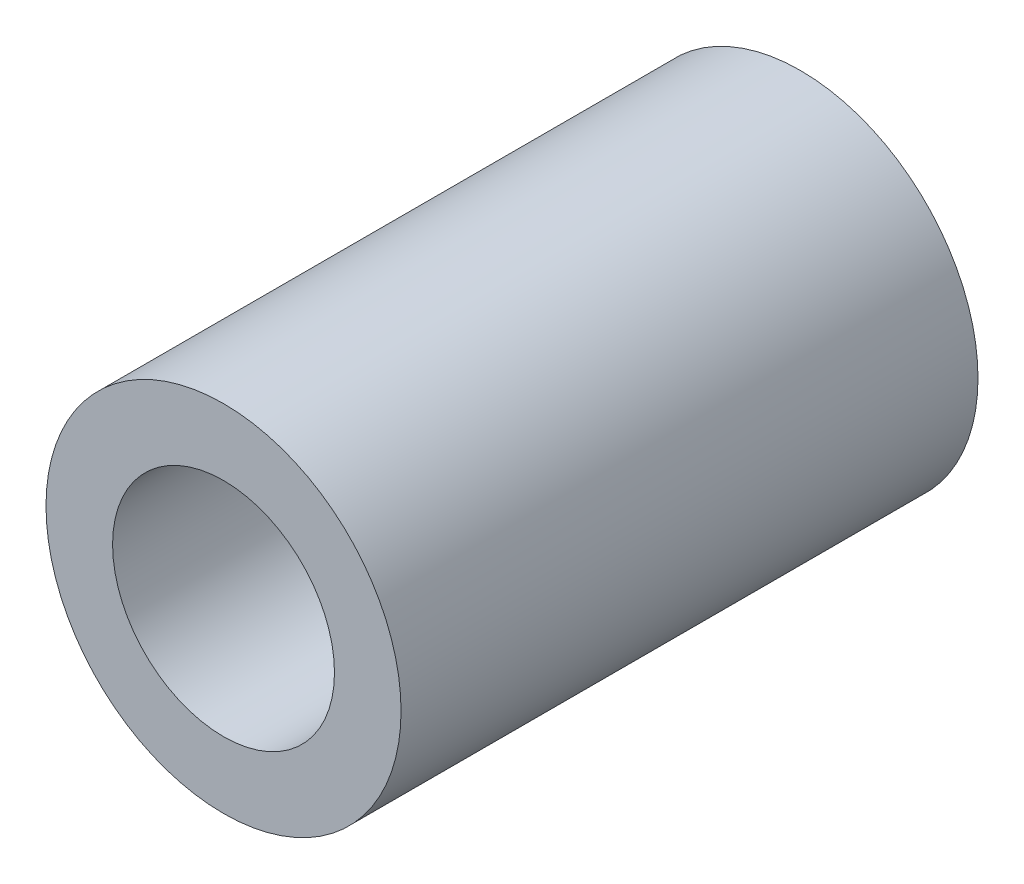
SolidWorks part; units mm, degrees
material "1.4021 (X20Cr13)"
ref_plane "Piano frontale" through (0, 0, 0) normal (0, 0, 1) x (1, 0, 0)
ref_plane "Piano superiore" through (0, 0, 0) normal (0, 1, 0) x (1, 0, 0)
ref_plane "Piano destro" through (0, 0, 0) normal (1, 0, 0) x (0, 0, -1)
sketch "Schizzo1" plane through (0, 0, 0) normal (0, 0, 1) x (1, 0, 0)
  circle A0 centre (0, 0) radius 4
  circle A1 centre (0, 0) radius 2.5
  dimension "D1" = 8
  dimension "D2" = 5
extrude "Estrusione-Estrusione1" add sketch "Schizzo1" against normal blind 13
